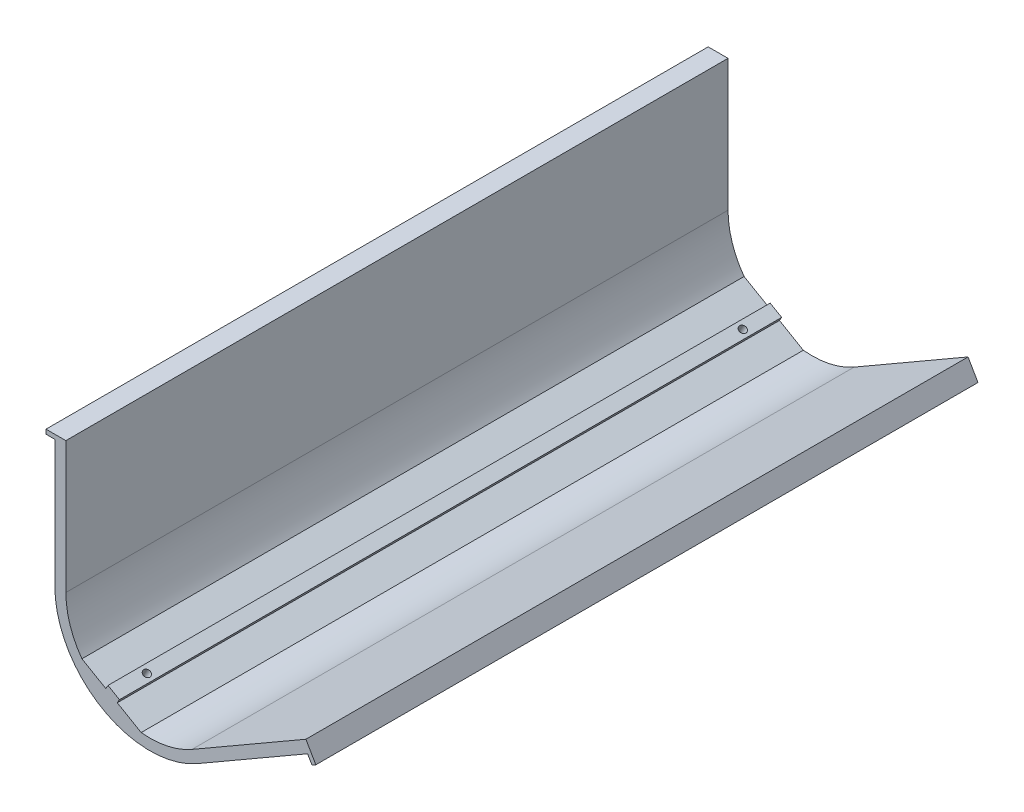
SolidWorks part; units mm, degrees
ref_plane "Front Plane" through (0, 0, 0) normal (0, 0, 1) x (1, 0, 0)
ref_plane "Top Plane" through (0, 0, 0) normal (0, 1, 0) x (1, 0, 0)
ref_plane "Right Plane" through (0, 0, 0) normal (1, 0, 0) x (0, 0, -1)
sketch "Sketch1" plane through (0, 0, 0) normal (0, 0, 1) x (1, 0, 0)
  line L0 (-10, 0) -> (-10, 46.9949) construction
  line L1 (-10, 420) -> (-10, 0) construction
  line L2 (-10.5, 54.093) -> (-10.5, 57.093) construction
  line L3 (-10.5, 57.093) -> (-14.5, 57.093) construction
  line L4 (-14.5, 57.093) -> (-14.5, 60.093) construction
  line L5 (-14.5, 60.093) -> (-4.5, 60.093) construction
  line L6 (-4.5, 60.093) -> (-4.5, 63.093) construction
  line L7 (95.3398, -13.8231) -> (54.641, -37.3205) construction
  line L8 (54.641, -37.3205) -> (418.3717, 172.6795) construction
  line L9 (-10, 0) -> (-10, 46.9949)
  line L10 (-10, 420) -> (-10, 0)
  line L11 (-10.5, 54.093) -> (-10.5, 57.093)
  line L12 (-10.5, 57.093) -> (-14.5, 57.093)
  line L13 (-14.5, 57.093) -> (-14.5, 60.093)
  line L14 (-14.5, 60.093) -> (-4.5, 60.093)
  line L15 (-4.5, 60.093) -> (-4.5, 63.093)
  line L16 (95.3398, -13.8231) -> (54.641, -37.3205)
  line L17 (54.641, -37.3205) -> (418.3717, 172.6795)
  line L18 (7.4103, -25.3516) -> (13.3139, -28.7601) construction
  line L19 (7.4103, -25.3516) -> (13.3139, -28.7601)
  arc A0 (-10, 0) -> (54.641, -37.3205) centre (33.094, 0) ccw construction
  arc A1 (-10, 0) -> (54.641, -37.3205) centre (33.094, 0) ccw
sketch "Sketch2" plane through (0, 0, 0) normal (0, 0, 1) x (1, 0, 0)
  line L0 (-10, 0) -> (-10, 46.9949) construction
  line L1 (-10, 0) -> (-10, 57.593)
  line L2 (-10, 420) -> (-10, 0) construction
  line L6 (-5, 0) -> (-5, 59.593)
  line L7 (-5, 0) -> (-5, 57.593) construction
  line L8 (-10, 59.593) -> (-5, 59.593)
  line L9 (-14, 59.593) -> (-4.5, 59.593)
  line L10 (-14, 57.593) -> (-14, 59.593)
  line L11 (-10.5, 57.593) -> (-14, 57.593)
  line L12 (-14, 59.593) -> (-10, 59.593)
  line L13 (-14, 57.593) -> (-14, 59.593)
  line L14 (-10, 57.593) -> (-14, 57.593)
  line L15 (11.547, -37.3205) -> (14.8632, -31.5767) construction
  line L16 (54.641, -37.3205) -> (104.518, -8.524)
  line L17 (104.518, -8.524) -> (106.518, -11.9881)
  line L18 (106.518, -11.9881) -> (108.2501, -10.9881)
  line L19 (108.2501, -10.9881) -> (106.2501, -7.524)
  line L20 (106.2501, -7.524) -> (103.7501, -3.1939)
  line L21 (52.141, -32.9904) -> (103.7501, -3.1939)
  line L22 (7.4103, -25.3516) -> (13.3139, -28.7601) construction
  line L23 (2.2701, -22.3839) -> (29.1209, -37.8863)
  arc A0 (-10, 0) -> (54.641, -37.3205) centre (33.094, 0) ccw construction
  arc A1 (-10, 0) -> (54.641, -37.3205) centre (33.094, 0) ccw
  arc A2 (-5, 0) -> (2.2701, -22.3839) centre (33.094, 0) ccw
  arc A3 (-5, 0) -> (52.141, -32.9904) centre (33.094, 0) ccw construction
  arc A4 (-10, 0) -> (54.641, -37.3205) centre (33.094, 0) ccw construction
  arc A5 (29.1209, -37.8863) -> (52.141, -32.9904) centre (33.094, 0) ccw
  dimension "D1" = 0.5
  dimension "D2" = 5
extrude "Boss-Extrude1" add sketch "Sketch2" along normal up to surface (300 mm away)
sketch "Sketch3" plane through (-9.125, -15.805, 0) normal (0.5, 0.866, 0) x (0.866, -0.5, 0)
  line L0 (28.6603, 0) -> (28.6603, -300) construction
  line L1 (44.1626, 0) -> (13.1579, 0) construction
  line L2 (44.1626, -300) -> (13.1579, -300) construction
  line L3 (28.6603, -150) -> (18.3372, -150) construction
  circle A0 centre (28.6603, -15) radius 1.6
  circle A1 centre (28.6603, -285) radius 1.6
  dimension "D1" = 3.2
  dimension "D2" = 15
extrude "Cut-Extrude1" cut sketch "Sketch3" against normal through all
sketch "Sketch4" plane through (-9.125, -15.805, 0) normal (0.5, 0.866, 0) x (0.866, -0.5, 0)
  circle A0 centre (28.6603, -15) radius 2.875
  circle A1 centre (28.6603, -285) radius 2.875
  dimension "D1" = 5.75
extrude "Cut-Extrude2" cut sketch "Sketch4" against normal through all from offset 2 offset against normal yes
sketch "Sketch5" plane through (-9.125, -15.805, 0) normal (0.5, 0.866, 0) x (0.866, -0.5, 0)
  line L0 (28.6603, 0) -> (28.6603, -300) construction
  line L1 (44.1626, 0) -> (13.1579, 0) construction
  line L2 (44.1626, -300) -> (13.1579, -300) construction
  line L4 (31.6603, -300) -> (25.6603, -300)
  line L5 (31.6603, -300) -> (31.6603, 0)
  line L6 (31.6603, 0) -> (25.6603, 0)
  line L7 (25.6603, -300) -> (25.6603, 0)
  line L8 (31.6603, -300) -> (25.6603, 0) construction
  line L9 (31.6603, 0) -> (25.6603, -300) construction
  circle A0 centre (28.6603, -15) radius 1.6 construction
  circle A1 centre (28.6603, -285) radius 1.6 construction
  circle A2 centre (28.6603, -15) radius 1.6
  circle A3 centre (28.6603, -285) radius 1.6
  point P6 (28.6603, -150)
  dimension "D1" = 6
extrude "Boss-Extrude2" add sketch "Sketch5" along normal blind 2
equation "\"m3screwdiameter\"=3.2"
equation "\"D1@Sketch3\"=\"m3screwdiameter\""
equation "\"M3Capheaddiameter\"=5.75"
equation "\"D1@Sketch4\"=\"M3Capheaddiameter\""
